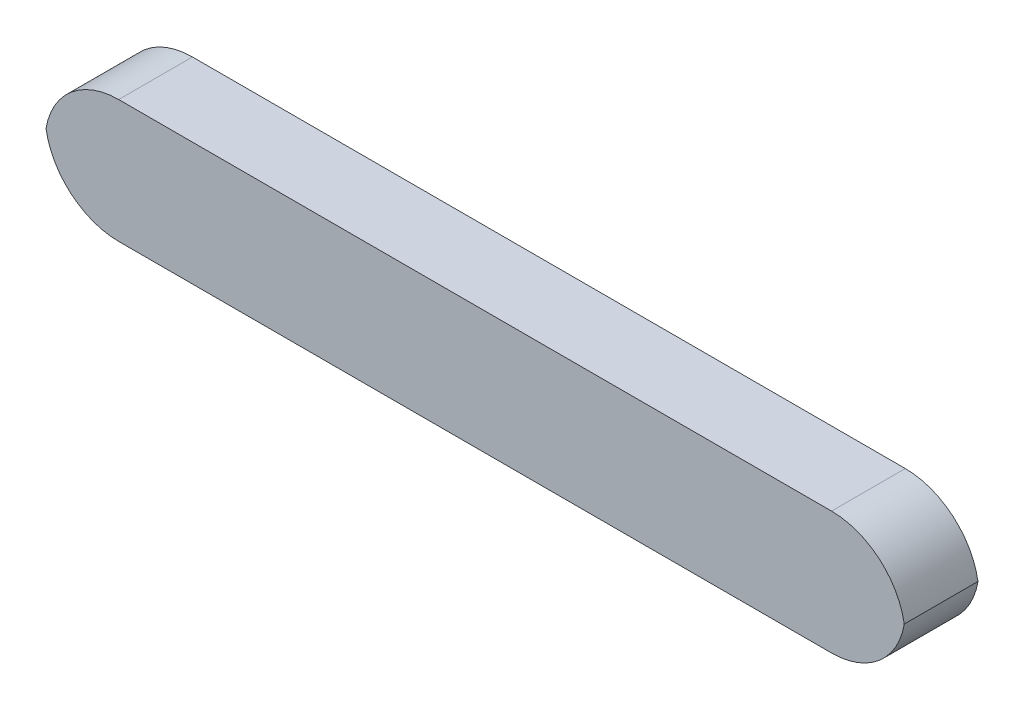
SolidWorks part; units mm, degrees
ref_plane "Alzado" through (0, 0, 0) normal (0, 0, 1) x (1, 0, 0)
ref_plane "Planta" through (0, 0, 0) normal (0, 1, 0) x (1, 0, 0)
ref_plane "Vista lateral" through (0, 0, 0) normal (1, 0, 0) x (0, 0, -1)
sketch "Croquis1" plane through (0, 0, 0) normal (0, 0, 1) x (1, 0, 0)
  line L1 (145, -25) -> (-145, -25)
  line L2 (175, 5) -> (175, -5)
  line L3 (145, 25) -> (-145, 25)
  line L4 (-175, 5) -> (-175, -5)
  line L5 (175, -25) -> (-175, 25) construction
  line L6 (175, 25) -> (-175, -25) construction
  arc A2 (175, 5) -> (145, -25) centre (145, 5) cw
  arc A3 (175, -5) -> (145, 25) centre (145, -5) ccw
  arc A4 (-175, 5) -> (-145, -25) centre (-145, 5) ccw
  arc A5 (-145, 25) -> (-175, -5) centre (-145, -5) ccw
  point P0 (0, 0)
  dimension "D2" = 30
  dimension "D1" = 350
  dimension "D3" = 50
extrude "Saliente-Extruir1" add sketch "Croquis1" along normal blind 30 contours L3 A5 A4 L1 A2 A3
